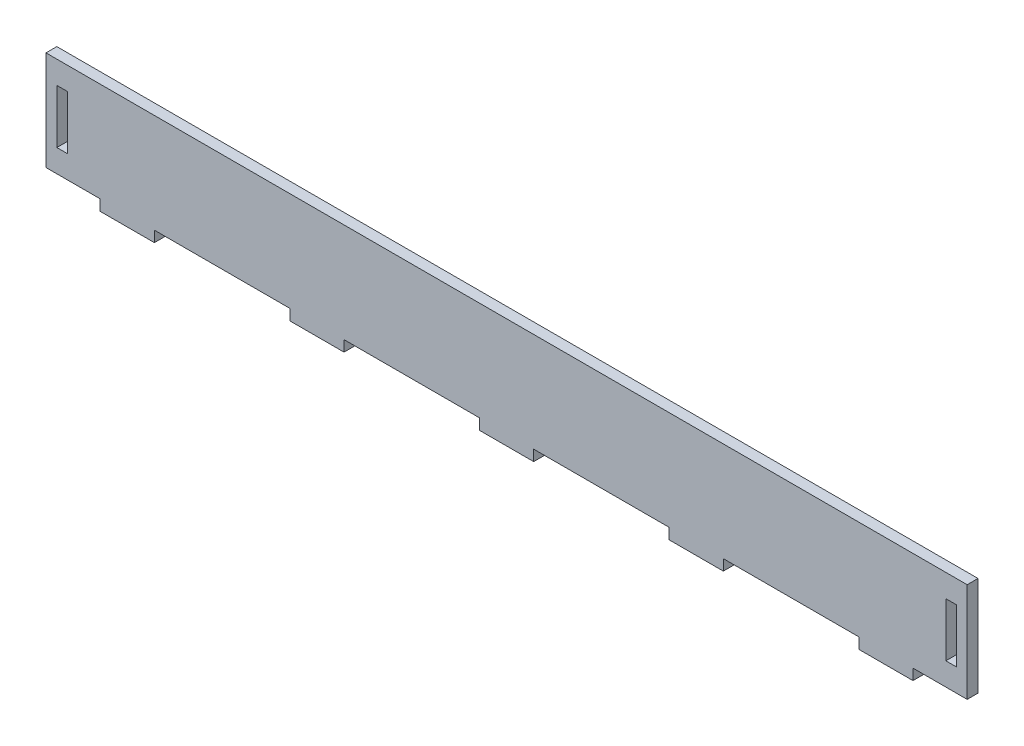
SolidWorks part; units mm, degrees
ref_plane "Alzado" through (0, 0, 0) normal (0, 0, 1) x (1, 0, 0)
ref_plane "Planta" through (0, 0, 0) normal (0, 1, 0) x (1, 0, 0)
ref_plane "Vista lateral" through (0, 0, 0) normal (1, 0, 0) x (0, 0, -1)
sketch "Croquis1" plane through (0, 0, 0) normal (0, 0, 1) x (1, 0, 0)
  line L1 (-255, -27.5) -> (255, -27.5)
  line L2 (-255, -27.5) -> (-255, 27.5)
  line L3 (-255, 27.5) -> (255, 27.5)
  line L4 (255, -27.5) -> (255, 27.5)
  line L5 (-255, -27.5) -> (255, 27.5) construction
  line L6 (-255, 27.5) -> (255, -27.5) construction
  point P0 (0, 0)
  dimension "D1" = 55
  dimension "D2" = 510
extrude "Saliente-Extruir1" add sketch "Croquis1" along normal blind 6
sketch "Croquis2" plane through (0, 0, 6) normal (0, 0, 1) x (1, 0, 0)
  line L0 (-255, 27.5) -> (-255, -27.5) construction
  line L1 (-243.2, -14.9) -> (-249, -14.9)
  line L2 (-243.2, -14.9) -> (-243.2, 14.9)
  line L3 (-243.2, 14.9) -> (-249, 14.9)
  line L4 (-249, -14.9) -> (-249, 14.9)
  line L5 (-243.2, -14.9) -> (-249, 14.9) construction
  line L6 (-243.2, 14.9) -> (-249, -14.9) construction
  line L7 (249, -14.9) -> (243.2, -14.9)
  line L8 (249, -14.9) -> (249, 14.9)
  line L9 (249, 14.9) -> (243.2, 14.9)
  line L10 (243.2, -14.9) -> (243.2, 14.9)
  line L11 (249, -14.9) -> (243.2, 14.9) construction
  line L12 (249, 14.9) -> (243.2, -14.9) construction
  line L13 (255, -27.5) -> (255, 27.5) construction
  point P0 (-246.1, 0)
  point P5 (246.1, 0)
  point P12 (0, 0)
  point P13 (-255, 0)
  point P16 (0, 0)
  point P17 (255, 0)
  dimension "D1" = 29.8
  dimension "D2" = 6
  dimension "D3" = 5.8
  dimension "D4" = 29.8
  dimension "D5" = 6
  dimension "D6" = 5.8
extrude "Cortar-Extruir1" cut sketch "Croquis2" against normal up to next
sketch "Croquis3" plane through (0, -27.5, 0) normal (0, -1, 0) x (1, 0, 0)
  line L0 (-255, 6) -> (255, 6) construction
  line L1 (-15, 6) -> (15, 6)
  line L2 (-15, 6) -> (-15, 0)
  line L3 (-15, 0) -> (15, 0)
  line L4 (15, 6) -> (15, 0)
  line L5 (-255, 0) -> (255, 0) construction
  line L7 (90, 6) -> (120, 6)
  line L8 (90, 6) -> (90, 0)
  line L9 (90, 0) -> (120, 0)
  line L10 (120, 6) -> (120, 0)
  line L11 (255, 6) -> (255, 0) construction
  line L12 (195, 6) -> (225, 6)
  line L13 (195, 6) -> (195, 0)
  line L14 (195, 0) -> (225, 0)
  line L15 (225, 6) -> (225, 0)
  line L16 (-255, 6) -> (-255, 0) construction
  line L17 (-90, 6) -> (-120, 6)
  line L18 (-90, 6) -> (-90, 0)
  line L19 (-90, 0) -> (-120, 0)
  line L20 (-120, 6) -> (-120, 0)
  line L21 (-195, 6) -> (-225, 6)
  line L22 (-195, 6) -> (-195, 0)
  line L23 (-195, 0) -> (-225, 0)
  line L24 (-225, 6) -> (-225, 0)
  point P8 (0, 6)
  point P21 (105, 6)
  point P30 (-105, 6)
  dimension "D1" = 30
  dimension "D2" = 30
  dimension "D3" = 30
  dimension "D4" = 30
  dimension "D5" = 90
  dimension "D6" = 30
  dimension "D7" = 90
  dimension "D8" = 30
  dimension "D9" = 30
extrude "Saliente-Extruir2" add sketch "Croquis3" along normal blind 6
